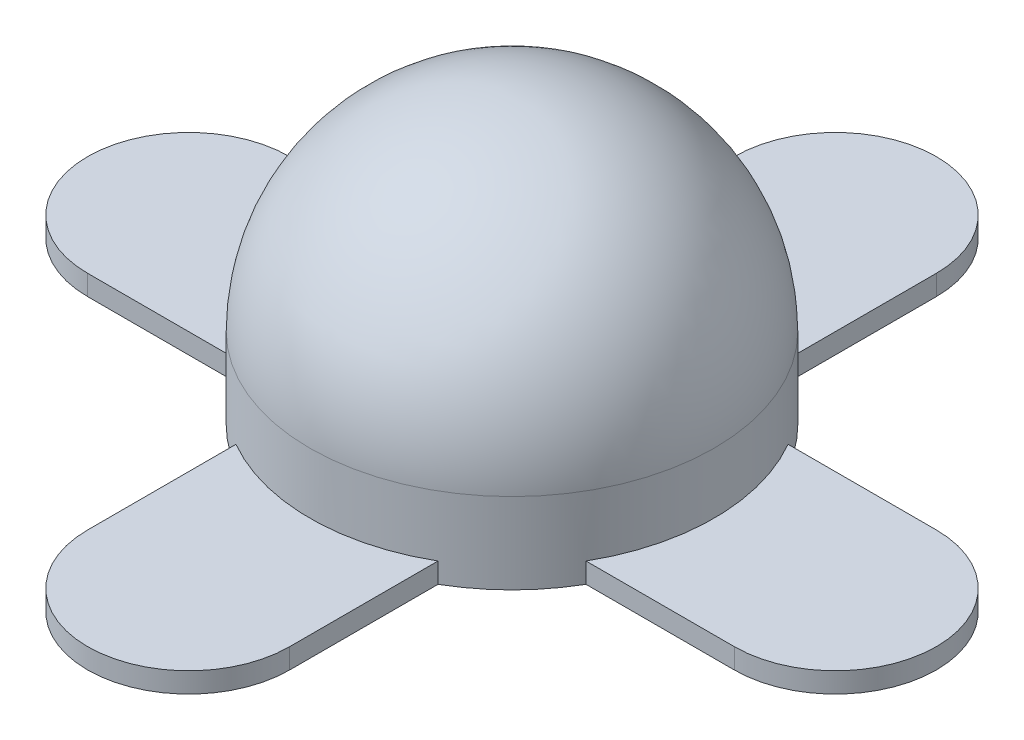
SolidWorks part; units mm, degrees
ref_plane "Front Plane" through (0, 0, 0) normal (0, 0, 1) x (1, 0, 0)
ref_plane "Top Plane" through (0, 0, 0) normal (0, 1, 0) x (1, 0, 0)
ref_plane "Right Plane" through (0, 0, 0) normal (1, 0, 0) x (0, 0, -1)
sketch "Sketch1" plane through (0, 0, 0) normal (0, 1, 0) x (1, 0, 0)
  circle A0 centre (0, 0) radius 5
  dimension "D1" = 10
extrude "Boss-Extrude1" add sketch "Sketch1" along normal blind 7
fillet "Fillet1" radius 5 1 edges at (0, 7, 5)
sketch "Esquisse1" plane through (0, 0, 0) normal (0, -1, 0) x (1, 0, 0)
  line L0 (-2.5, 4.3301) -> (-2.5, 8)
  line L1 (2.5, 8) -> (2.5, 4.3301)
  line L2 (0, 0) -> (0, 10.993) construction
  line L3 (4.3301, 2.5) -> (8, 2.5)
  line L4 (8, -2.5) -> (4.3301, -2.5)
  line L5 (2.5, -4.3301) -> (2.5, -8)
  line L6 (-2.5, -8) -> (-2.5, -4.3301)
  line L7 (-4.3301, -2.5) -> (-8, -2.5)
  line L8 (-8, 2.5) -> (-4.3301, 2.5)
  circle A0 centre (0, 0) radius 5 construction
  arc A1 (-2.5, 8) -> (2.5, 8) centre (0, 8) cw
  arc A2 (8, 2.5) -> (8, -2.5) centre (8, 0) cw
  arc A3 (2.5, -8) -> (-2.5, -8) centre (0, -8) cw
  arc A4 (-8, -2.5) -> (-8, 2.5) centre (-8, 0) cw
  circle A5 centre (0, 0) radius 5
  point P28 (0, 0)
  circle M4 centre (0, 0) radius 5
  dimension "D1" = 5
  dimension "D2" = 8
  dimension "D3" = 4
extrude "Boss.-Extru.1" add sketch "Esquisse1" against normal blind 0.5 contours A2 L3 L4 M4 | L2 L1 A1 M4 | A5 L2 A1 L0 | A4 L7 L8 M4 | A3 L5 L6 M4
